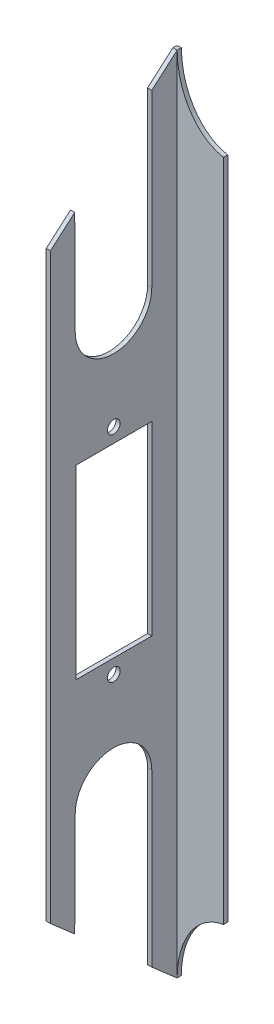
SolidWorks part; units mm, degrees
material "1.0545 (S355N)"
ref_plane "Płaszczyzna przednia" through (0, 0, 0) normal (0, 0, 1) x (1, 0, 0)
ref_plane "Płaszczyzna górna" through (0, 0, 0) normal (0, 1, 0) x (1, 0, 0)
ref_plane "Płaszczyzna prawa" through (0, 0, 0) normal (1, 0, 0) x (0, 0, -1)
ref_plane "Płaszczyzna1" through (907.5, 0, 0) normal (-1, 0, 0) x (0, 0, 1)
sketch "Szkic1" plane through (907.5, 0, 0) normal (-1, 0, 0) x (0, 0, 1)
  line L0 (1130.3483, 95.1439) -> (1130.3483, -95.1439)
  line L1 (1160.3483, 68.9811) -> (1130.3483, 95.1439)
  line L4 (1160.3483, -25.4) -> (1160.3483, 25.4)
  line L5 (1130.3483, 25.4) -> (1130.3483, -25.4)
  line L6 (1160.3483, 68.9811) -> (1160.3483, -68.9811)
  line L7 (1160.3483, -68.9811) -> (1130.3483, -95.1439)
  line L9 (1154.3483, 22) -> (1136.3483, 22)
  line L10 (1154.3483, 22) -> (1154.3483, -22)
  line L11 (1154.3483, -22) -> (1136.3483, -22)
  line L12 (1136.3483, 22) -> (1136.3483, -22)
  arc A4 (1160.3483, 25.4) -> (1130.3483, 25.4) centre (1145.3483, 25.4) ccw
  arc A5 (1130.3483, -25.4) -> (1160.3483, -25.4) centre (1145.3483, -25.4) ccw
  circle A6 centre (1145.3483, 25.4) radius 1.5
  circle A7 centre (1145.3483, -25.4) radius 1.5
ref_plane "Płaszczyzna2" through (0, 0, 1160.3483) normal (0, 0, 1) x (1, 0, 0)
ref_plane "Płaszczyzna3" through (0, 0, 1130.3483) normal (0, 0, -1) x (-1, 0, 0)
sketch "Szkic3" plane through (0, 0, 1160.3483) normal (0, 0, 1) x (1, 0, 0)
  spline S2 degree 3 poles (926.8738, 42.6304) (925.8192, 41.1478) (925.4467, 40.6719) (924.8453, 39.9952) (924.6376, 39.7759) (924.2047, 39.3526) (923.9787, 39.148) (923.2781, 38.5715) (922.7799, 38.2333) (921.9592, 37.8342) (921.6758, 37.7212) (921.0981, 37.5471) (920.8022, 37.4851) (920.194, 37.4194) (919.8916, 37.4169) (919.292, 37.47) (918.9927, 37.5261) (918.1129, 37.7747) (917.5709, 38.0379) (916.547, 38.6959) (916.0818, 39.08) (915.2156, 39.913) (914.8122, 40.3654) (914.0579, 41.3096) (913.709, 41.7984) (913.0524, 42.8003) (912.7449, 43.3135) (912.1629, 44.3593) (911.8886, 44.8921) (911.368, 45.9742) (911.1213, 46.5249) (910.4238, 48.1881) (910.0148, 49.3108) (909.2899, 51.5794) (908.9743, 52.7253) (908.431, 55.039) (908.2033, 56.2067) (907.9294, 57.9752) (907.8494, 58.5675) (907.713, 59.7579) (907.6564, 60.3573) (907.5247, 62.1549) (907.4871, 63.3505) (907.5208, 65.7353) (907.5919, 66.9246) (907.8593, 69.296) (908.0557, 70.4804) (908.6006, 72.8306) (908.9448, 73.9796) (909.5918, 75.6554) (909.8294, 76.206) (910.355, 77.2889) (910.6444, 77.823) (911.5841, 79.3643) (912.3068, 80.3197) (913.3752, 81.3903) (913.5975, 81.5981) (914.0535, 81.9936) (914.2879, 82.182) (915.0119, 82.7179) (915.5219, 83.0361) (916.3353, 83.4438) (916.6138, 83.5674) (917.1764, 83.7849) (917.4618, 83.8793) (918.041, 84.0386) (918.3348, 84.1035) (918.9314, 84.2021) (919.2358, 84.2358) (920.1414, 84.2861) (920.7406, 84.254) (921.6327, 84.11) (921.9304, 84.0455) (922.5166, 83.8861) (922.8036, 83.7918) (923.6471, 83.4681) (924.1877, 83.1975) (925.2229, 82.5601) (925.7055, 82.2013) (926.6126, 81.4172) (927.0371, 80.9919) (927.6354, 80.3098) (927.8283, 80.0751) (928.1972, 79.5982) (928.3739, 79.3552) (929.2219, 78.1194) (929.7886, 77.0657) (930.5095, 75.4095) (930.7277, 74.8444) (931.1183, 73.7096) (931.2917, 73.1375) (931.7543, 71.4088) (931.9861, 70.2398) (932.2379, 68.4656) (932.3057, 67.8708) (932.4112, 66.6745) (932.4487, 66.0727) (932.5177, 64.2762) (932.5067, 63.0844) (932.3248, 59.5243) (932.0076, 57.1709) (931.3866, 54.2522) (931.2509, 53.6696) (930.9561, 52.5069) (930.797, 51.9273) (930.2876, 50.2065) (929.9042, 49.0785) (929.0403, 46.8649) (928.5603, 45.7792) (927.4759, 43.6623) (926.8738, 42.6304) (925.8192, 41.1478) (925.4467, 40.6719) knots -0.03125 -0.03125 0 0 0.015625 0.015625 0.023438 0.023438 0.03125 0.03125 0.046875 0.046875 0.054688 0.054688 0.0625 0.0625 0.070313 0.070313 0.078125 0.078125 0.09375 0.09375 0.109375 0.109375 0.125 0.125 0.140625 0.140625 0.15625 0.15625 0.171875 0.171875 0.1875 0.1875 0.21875 0.21875 0.25 0.25 0.28125 0.28125 0.296875 0.296875 0.3125 0.3125 0.34375 0.34375 0.375 0.375 0.40625 0.40625 0.4375 0.4375 0.453125 0.453125 0.46875 0.46875 0.5 0.5 0.507813 0.507813 0.515625 0.515625 0.53125 0.53125 0.539063 0.539063 0.546875 0.546875 0.554688 0.554688 0.5625 0.5625 0.578125 0.578125 0.585938 0.585938 0.59375 0.59375 0.609375 0.609375 0.625 0.625 0.640625 0.640625 0.648438 0.648438 0.65625 0.65625 0.6875 0.6875 0.703125 0.703125 0.71875 0.71875 0.75 0.75 0.765625 0.765625 0.78125 0.78125 0.8125 0.8125 0.875 0.875 0.890625 0.890625 0.90625 0.90625 0.9375 0.9375 0.96875 0.96875 1 1 1.015625 1.015625 1.023438 only from (926.1707, 41.642) to (926.1707, 41.642)
  spline S3 degree 3 poles (915.9951, -83.2782) (915.1927, -82.8367) (914.6938, -82.4994) (913.755, -81.7544) (913.3152, -81.3466) (912.4873, -80.4692) (912.0986, -79.9977) (911.3869, -79.026) (911.0608, -78.5227) (910.4593, -77.4865) (910.1839, -76.9536) (909.6782, -75.8614) (909.4472, -75.2997) (908.8239, -73.6016) (908.4987, -72.4501) (907.9902, -70.1166) (907.8074, -68.9345) (907.625, -67.1416) (907.5796, -66.5391) (907.5185, -65.3373) (907.5026, -64.7379) (907.4911, -61.7478) (907.6946, -59.3778) (908.2695, -55.8505) (908.5069, -54.6794) (908.9329, -52.93) (909.0868, -52.3473) (909.4168, -51.1919) (909.593, -50.6186) (910.1563, -48.9122) (910.5776, -47.7924) (911.2908, -46.1444) (911.5422, -45.6004) (912.0766, -44.5248) (912.3603, -43.992) (912.9628, -42.9479) (913.2811, -42.437) (913.9611, -41.4437) (914.3243, -40.9591) (915.101, -40.04) (915.5135, -39.6056) (916.1844, -39.0086) (916.4169, -38.8188) (916.904, -38.4625) (917.1598, -38.2955) (917.6864, -37.9996) (917.9582, -37.8696) (918.5231, -37.6535) (918.8178, -37.5676) (919.4083, -37.4539) (919.7065, -37.4248) (920.3093, -37.4259) (920.6156, -37.457) (921.2077, -37.5741) (921.4968, -37.6599) (922.0628, -37.8789) (922.3373, -38.0116) (923.1225, -38.4568) (923.6056, -38.82) (924.5085, -39.6271) (924.9203, -40.0635) (925.6914, -40.9796) (926.0505, -41.4596) (926.7289, -42.4526) (927.0482, -42.9661) (927.6468, -44.0052) (927.9275, -44.5329) (928.7234, -46.1355) (929.1935, -47.2299) (930.0381, -49.46) (930.4123, -50.5957) (931.4033, -54.0595) (931.8764, -56.3904) (932.4604, -61.0911) (932.5717, -63.4614) (932.4258, -66.4557) (932.3819, -67.0573) (932.2634, -68.2522) (932.1887, -68.8466) (931.9154, -70.62) (931.6678, -71.7894) (931.1771, -73.5199) (930.993, -74.0944) (930.5817, -75.2266) (930.3555, -75.782) (929.6089, -77.413) (929.0222, -78.4542) (927.9611, -79.922) (927.5789, -80.3917) (926.7623, -81.2706) (926.3265, -81.6822) (925.6238, -82.2503) (925.3804, -82.432) (924.8804, -82.7736) (924.6248, -82.933) (923.84, -83.3753) (923.2934, -83.6226) (922.4326, -83.9115) (922.1387, -83.9938) (921.5514, -84.1256) (921.2561, -84.1757) (920.3656, -84.2787) (919.7641, -84.2841) (918.5538, -84.1616) (917.9658, -84.036) (917.1068, -83.7603) (916.8244, -83.6538) (916.2671, -83.412) (915.9951, -83.2782) (915.1927, -82.8367) (914.6938, -82.4994) knots -0.007812 -0.007812 0 0 0.015625 0.015625 0.03125 0.03125 0.046875 0.046875 0.0625 0.0625 0.078125 0.078125 0.09375 0.09375 0.125 0.125 0.15625 0.15625 0.171875 0.171875 0.1875 0.1875 0.25 0.25 0.28125 0.28125 0.296875 0.296875 0.3125 0.3125 0.34375 0.34375 0.359375 0.359375 0.375 0.375 0.390625 0.390625 0.40625 0.40625 0.421875 0.421875 0.429687 0.429687 0.4375 0.4375 0.445312 0.445312 0.453125 0.453125 0.460937 0.460937 0.46875 0.46875 0.476562 0.476562 0.484375 0.484375 0.5 0.5 0.515625 0.515625 0.53125 0.53125 0.546875 0.546875 0.5625 0.5625 0.59375 0.59375 0.625 0.625 0.6875 0.6875 0.75 0.75 0.765625 0.765625 0.78125 0.78125 0.8125 0.8125 0.828125 0.828125 0.84375 0.84375 0.875 0.875 0.890625 0.890625 0.90625 0.90625 0.914062 0.914062 0.921875 0.921875 0.9375 0.9375 0.945312 0.945312 0.953125 0.953125 0.96875 0.96875 0.984375 0.984375 0.992188 0.992188 1 1 1.015625 1.015625 1.03125 only from (915.7276, -83.131) to (915.7276, -83.131)
sketch "Szkic4" plane through (0, 0, 1130.3483) normal (0, 0, -1) x (-1, 0, 0)
  spline S1 degree 3 poles (-920, -78.5582) (-945, -78.5582) (-945, -111.7296) (-920, -111.7296) (-895, -111.7296) (-895, -78.5582) (-920, -78.5582) (-945, -78.5582) (-945, -111.7296) knots -0.5 0 0 0 0.5 0.5 0.5 1 1 1 1.5 1.5 1.5 weights 1 0.333333 0.333333 1 0.333333 0.333333 1 0.333333 0.333333 only from (-920, -78.5582) to (-920, -78.5582)
  spline S3 degree 3 poles (-920, 111.7296) (-945, 111.7296) (-945, 78.5582) (-920, 78.5582) (-895, 78.5582) (-895, 111.7296) (-920, 111.7296) (-945, 111.7296) (-945, 78.5582) knots -0.5 0 0 0 0.5 0.5 0.5 1 1 1 1.5 1.5 1.5 weights 1 0.333333 0.333333 1 0.333333 0.333333 1 0.333333 0.333333 only from (-920, 111.7296) to (-920, 111.7296)
extrude "Dodanie-wyciągnięcie1" add sketch "Szkic1" along normal blind 1 contours A4 L6 L1 L0 | A5 L0 L7 L6 | L0 A5 L4 A4 A7 A6 L12 L9 L10 L11
ref_plane "Płaszczyzna4" through (0, 0, 1130.3483) normal (0, 0, -1) x (-1, 0, 0)
sketch "Szkic6" plane through (0, 0, 1130.3483) normal (0, 0, -1) x (-1, 0, 0)
  line L0 (-907.5, 95.1439) -> (-907.5, -95.1439)
  line L2 (-906.5, 95.1439) -> (-906.5, -95.1439) construction
  line L3 (-918.5, -78.678) -> (-918.5, 78.678)
  spline S1 degree 3 poles (-918.5, 78.678) (-912.6887, 79.6101) (-907.5, 85.3428) (-907.5, 95.1439) knots 0.528399 0.528399 0.528399 0.528399 0.75 0.75 0.75 0.75 weights 0.892857 0.630952 0.5 0.5
  spline S3 degree 3 poles (-907.5, -95.1439) (-907.5, -85.3428) (-912.6887, -79.6101) (-918.5, -78.678) knots 0.75 0.75 0.75 0.75 0.971601 0.971601 0.971601 0.971601 weights 0.5 0.5 0.630952 0.892857
extrude "Dodanie-wyciągnięcie2" add sketch "Szkic6" along normal blind 1 separate body
sketch "Szkic7" plane through (907.5, 0, 0) normal (-1, 0, 0) x (0, 0, 1)
  line L0 (1129.3483, -95.1439) -> (1129.3483, 94.308)
  line L1 (1129.3483, 94.308) -> (1129.3483, 95.1439)
  line L2 (1129.3483, 95.1439) -> (1130.3483, 95.1439)
  line L3 (1130.3483, 95.1439) -> (1130.3483, -95.1439)
  line L4 (1130.3483, -95.1439) -> (1129.3483, -95.1439)
  line L5 (1129.3483, 95.1439) -> (1130.3483, 95.1439) construction
extrude "Dodanie-wyciągnięcie3" add sketch "Szkic7" along normal blind 1 contours L4 L0 L1 L2 L3
fillet "Zaokrąglenie2" radius 0.5 1 edges at (906.5, 0, 1129.3483)
sketch "Szkic8" plane through (906.5, 0, 0) normal (-1, 0, 0) x (0, 0, 1)
  line L0 (1154.3483, 22) -> (1154.5994, 73.9947)
  line L1 (1160.3483, 68.9811) -> (1130.3483, 95.1439) construction
  line L2 (1136.3483, 22) -> (1136.3483, 89.9113)
  line L3 (1136.3483, 22) -> (1136.3483, -22) construction
  circle A0 centre (1145.3483, 25.4) radius 15
  arc A1 (1136.3483, 49.4662) -> (1154.4807, 49.4224) centre (1145.4145, 49.4662) ccw
  line M10 (1160.3483, 68.9811) -> (1130.3483, 95.1439)
  dimension "D1" = 30
extrude "Wytnij-wyciągnięcie1" cut sketch "Szkic8" against normal blind 1 contours L2 A1 L0 M10
mirror "Lustro1" about plane through (0, 0, 0) normal (0, 1, 0) of "Wytnij-wyciągnięcie1"
